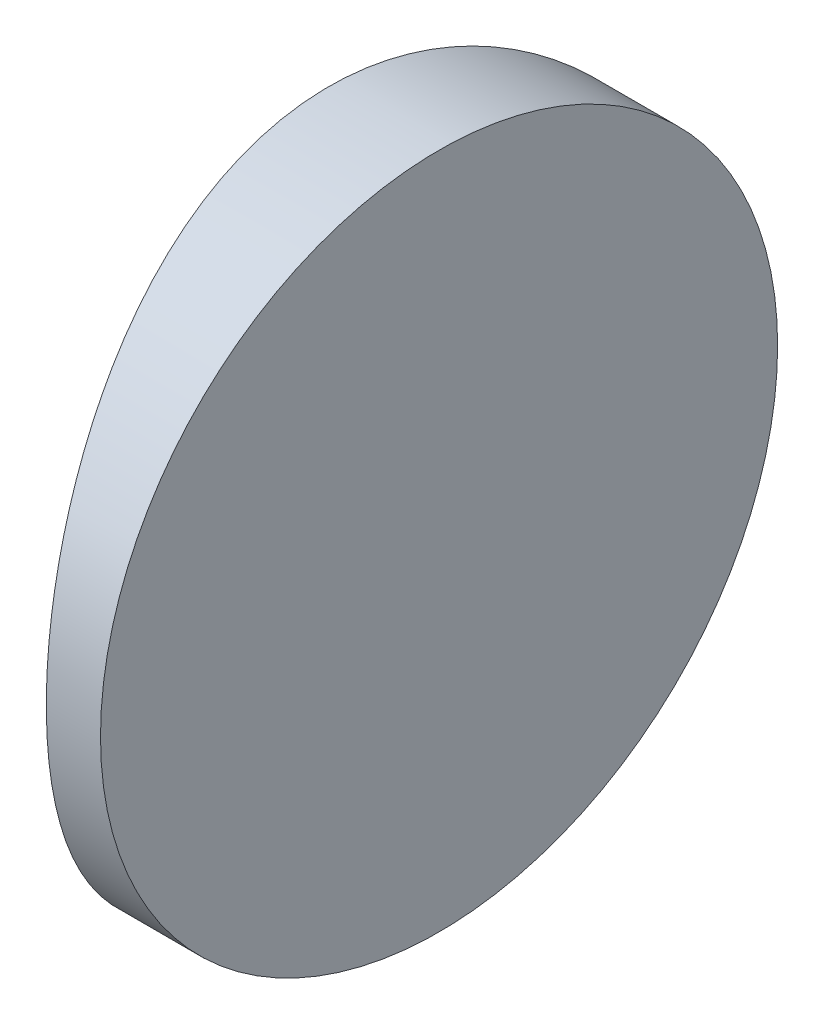
SolidWorks part; units mm, degrees
ref_plane "前视基准面" through (0, 0, 0) normal (0, 0, 1) x (1, 0, 0)
ref_plane "上视基准面" through (0, 0, 0) normal (0, 1, 0) x (1, 0, 0)
ref_plane "右视基准面" through (0, 0, 0) normal (1, 0, 0) x (0, 0, -1)
sketch "草图1" plane through (0, 0, 0) normal (0, 1, 0) x (1, 0, 0)
  line L0 (10.7432, 0) -> (-55.502, 0) construction
  line L1 (-32.355, 12.5) -> (-30.3548, 12.5)
  line L2 (-32.355, -12.5) -> (-30.3548, -12.5)
  line L3 (-30.3548, 12.5) -> (-30.3548, -12.5)
  arc A0 (-32.355, 12.5) -> (-32.355, -12.5) centre (4.3552, 0) ccw
  point P19 (-34.4248, 0)
  point P20 (-30.3548, 0)
  dimension "D2" = 12.5
  dimension "D3" = 38.78
  dimension "D4" = 4.07
  dimension "D1" = 12.5
extrude "凸台-拉伸1" add sketch "草图1" along normal blind 25 contours A0 L2 L3 L1
sketch "草图2" plane through (-30.3548, 0, 0) normal (1, 0, 0) x (0, 0, -1)
  line L0 (12.5, 0) -> (-12.5, 0) construction
  line L7 (-12.5, 0) -> (12.5, 0)
  line L8 (12.5, 0) -> (12.5, 25)
  line L9 (12.5, 25) -> (-12.5, 25)
  line L10 (-12.5, 25) -> (-12.5, 0)
  line L11 (-12.5, 0) -> (12.5, 0)
  line L12 (12.5, 0) -> (12.5, 25)
  line L13 (12.5, 25) -> (-12.5, 25)
  line L14 (-12.5, 25) -> (-12.5, 0)
  circle A0 centre (0, 12.5) radius 12.5
  line M1 (-12.5, 0) -> (12.5, 0)
  line M2 (12.5, 0) -> (12.5, 25)
  line M3 (12.5, 25) -> (-12.5, 25)
  line M4 (-12.5, 25) -> (-12.5, 0)
  dimension "D1" = 25
  dimension "D4" = 12.5
  dimension "D2" = 12.5
  dimension "D3" = 0
extrude "切除-拉伸8" cut sketch "草图2" against normal blind 12.7 contours A0 L13 M4 | A0 L12 M3 | A0 L11 M2 | A0 L14 M1
